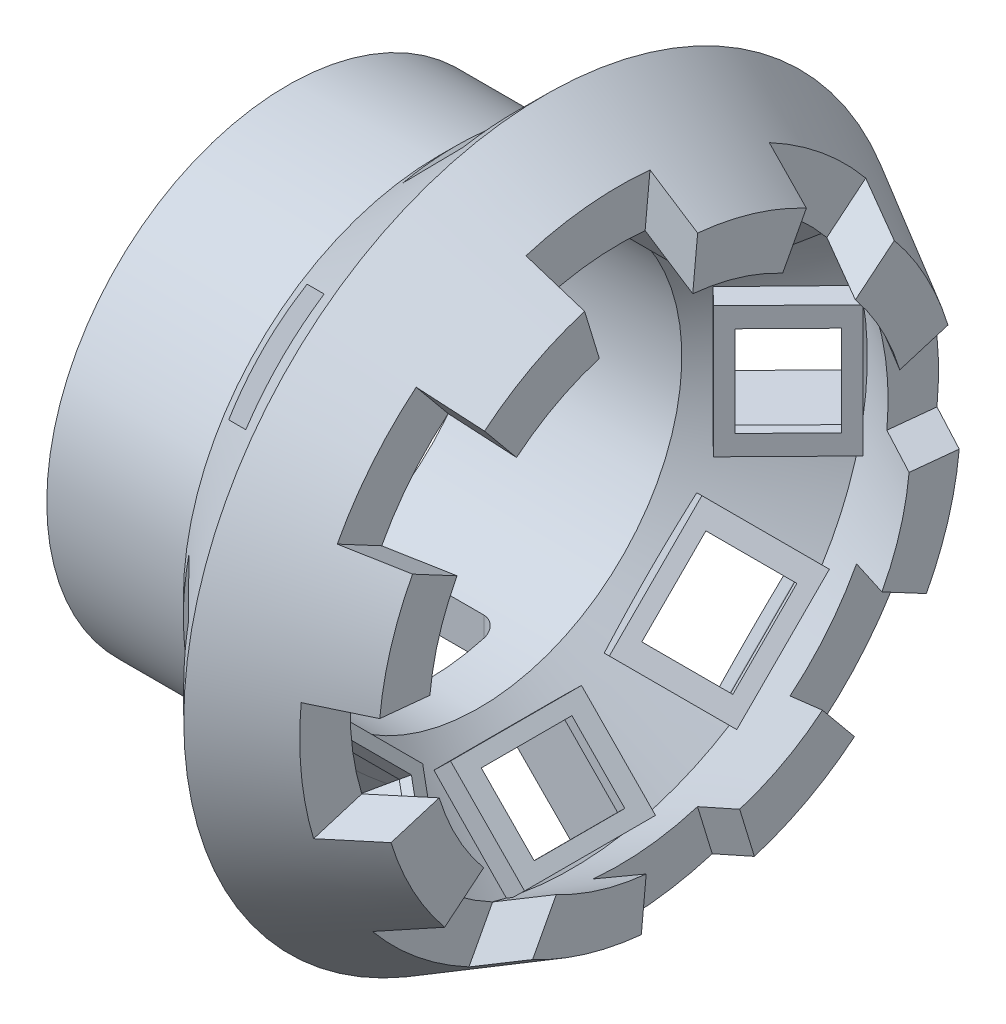
SolidWorks part; units mm, degrees
other "标注1"
sketch "草图8" plane through (-2.7147, -6.8585, 6.8585) normal (-0.2235, -0.0225, 0.9745) x (-0.1799, 0.9835, -0.0185)
ref_plane "前视基准面" through (0, 0, 0) normal (0, 0, 1) x (1, 0, 0)
ref_plane "上视基准面" through (0, 0, 0) normal (0, 1, 0) x (1, 0, 0)
ref_plane "右视基准面" through (0, 0, 0) normal (1, 0, 0) x (0, 0, -1)
sketch "草图1" plane through (0, 0, 0) normal (0, 0, 1) x (1, 0, 0)
  line L7 (8.0647, 7.1695) -> (11.04, 5.5)
  line L8 (11.04, 5.5) -> (11.04, 4.5)
  line L9 (11.04, 4.5) -> (8.6008, 5.8686)
  line L11 (7.54, 5.8) -> (7.54, 0) construction
  line L12 (0, 0) -> (8.3011, 0) construction
  line L13 (8.034, 5.3041) -> (7.54, 5.8) construction
  line L14 (6.755, 4.03) -> (8.6008, 5.8686)
  line L16 (11.04, 4.5) -> (11.04, -0.8919) construction
  line L17 (8.034, 5.3041) -> (11.109, 2.217) construction
  line L23 (5.955, 5.068) -> (8.0647, 7.1695)
  line L24 (6.0503, 4.03) -> (7.3502, 4.03) construction
  line L25 (5.955, 5.068) -> (5.955, 4.78)
  line L28 (6.0503, 4.03) -> (6.755, 4.03)
  line L31 (6.0503, 4.03) -> (2.955, 4.03)
  line L33 (5.955, 4.78) -> (2.955, 4.78)
  line L34 (2.955, 4.03) -> (2.955, 4.78)
  dimension "D1" = 4.5
  dimension "D2" = 3
  dimension "D3" = 0.8
  dimension "D4" = 4.03
  dimension "D5" = 0.8
  dimension "D6" = 0.7
  dimension "D7" = 5.8
  dimension "D8" = 1.3
  dimension "D9" = 1
  dimension "D10" = 3.5
  dimension "D13" = 0.75
revolve "旋转1" add sketch "草图1" angle 360 about L12
sketch "草图2" plane through (0, 0, 0) normal (0, 1, 0) x (1, 0, 0)
  line L1 (3.0145, -5.257) -> (4.0717, -5.257) construction
  line L8 (5.955, -5.068) -> (8.0647, -7.1695) construction
  line L9 (5.1803, -6.5082) -> (7.3988, -4.2897)
  line L10 (5.1803, -6.5082) -> (6.3824, -7.7103)
  line L11 (6.3824, -7.7103) -> (8.6009, -5.4918)
  line L12 (7.3988, -4.2897) -> (8.6009, -5.4918)
  line L13 (5.1803, -6.5082) -> (8.6009, -5.4918) construction
  line L14 (6.3824, -7.7103) -> (7.3988, -4.2897) construction
  line L15 (0, 0) -> (-4.3641, 0) construction
  line L16 (6.8906, -6) -> (5.7814, -7.1092) construction
  line L17 (5.955, -5.068) -> (8.0647, -7.1695) construction
  line L18 (5.955, -5.068) -> (8.0647, -7.1695) construction
  line L19 (5.955, -5.068) -> (8.0647, -7.1695) construction
  dimension "D1" = 45
  dimension "D2" = 1.7
  dimension "D3" = 6
extrude "切除-拉伸1" cut sketch "草图2" against normal mid plane 2.2
sketch "草图3" plane through (0, 0, 0) normal (0, 1, 0) x (1, 0, 0)
  line L0 (0, 0) -> (-2.7147, 0) construction
pattern_circular "阵列(圆周)1" count 8 over 360 about axis through (0, 0, 0) along (1, 0, 0) of "切除-拉伸1"
sketch "草图6" plane through (0, 0, 0) normal (0, 0, 1) x (1, 0, 0)
  line L0 (5.955, 5.068) -> (5.955, -5.068) construction
  line L1 (-2.939, 5.7136) -> (2.955, 5.7136)
  line L2 (-2.939, 5.7136) -> (-2.939, -5.5135)
  line L3 (-2.939, -5.5135) -> (2.955, -5.5135)
  line L4 (2.955, 5.7136) -> (2.955, -5.5135)
  line L5 (10.54, 7.4147) -> (14.0576, 7.4147)
  line L6 (10.54, 7.4147) -> (10.54, -7.7149)
  line L7 (10.54, -7.7149) -> (14.0576, -7.7149)
  line L8 (14.0576, 7.4147) -> (14.0576, -7.7149)
  line L9 (11.04, -5.5) -> (11.04, 5.5) construction
  dimension "D1" = 3
  dimension "D2" = 0.5
extrude "切除-拉伸2" cut sketch "草图6" against normal mid plane 20
ref_plane "基准面3" through (1.5037, -1.4741, 0) normal (-0.7141, 0.7001, 0) x (0, 0, 1)
sketch "草图7" plane through (1.5037, -1.4741, 0) normal (-0.7141, 0.7001, 0) x (0, 0, 1)
  line L10 (1.3, 10.1446) -> (-1.3, 10.1446)
  line L32 (-1.3, 10.1446) -> (-1.3, 8.0445)
  line L33 (-1.3, 8.0445) -> (1.3, 8.0445)
  line L34 (1.3, 8.0445) -> (1.3, 10.1446)
  line L35 (1.1, 9.9446) -> (-1.1, 9.9446)
  line L36 (-1.1, 9.9446) -> (-1.1, 8.2445)
  line L37 (-1.1, 8.2445) -> (1.1, 8.2445)
  line L38 (1.1, 8.2445) -> (1.1, 9.9446)
  dimension "D1" = 0.2
  dimension "D2" = 0.2
  dimension "D3" = 0.2
  dimension "D4" = 0.2
extrude "凸台-拉伸1" add sketch "草图7" along normal mid plane 0.6
sketch "草图11" plane through (1.7179, -1.6841, 0) normal (0.7141, -0.7001, 0) x (0, 0, -1)
  line L1 (-1.3, 10.1446) -> (1.3, 10.1446)
  line L2 (-1.3, 10.1446) -> (-1.3, 8.0445)
  line L3 (-1.3, 8.0445) -> (1.3, 8.0445)
  line L4 (1.3, 10.1446) -> (1.3, 8.0445)
  line L9 (-0.9, 9.8446) -> (0.9, 9.8446)
  line L10 (-0.9, 9.8446) -> (-0.9, 8.3445)
  line L11 (-0.9, 8.3445) -> (0.9, 8.3445)
  line L12 (0.9, 9.8446) -> (0.9, 8.3445)
  line L14 (-1.1, 9.9446) -> (1.1, 9.9446) construction
  line L15 (1.1, 8.2445) -> (-1.1, 8.2445) construction
  dimension "D1" = 0.4
  dimension "D2" = 0.4
  dimension "D3" = 0.1
  dimension "D4" = 0.1
extrude "凸台-拉伸2" add sketch "草图11" along normal blind 0.2
pattern_circular "阵列(圆周)2" count 8 over 360 about axis through (0, 0, 0) along (1, 0, 0) of "凸台-拉伸1", "凸台-拉伸2"
sketch "草图9" plane through (10.54, 0, 0) normal (1, 0, 0) x (0, 0, -1)
  line L2 (0, 0) -> (-2.1978, 7.2108)
  line L3 (0, 0) -> (0.729, 7.503)
  line L4 (0, 0) -> (3.5447, 6.6529)
  line L5 (0, 0) -> (5.8208, 4.7899)
  line L6 (0, 0) -> (7.2108, 2.1978)
  line L7 (0, 0) -> (7.503, -0.729)
  line L8 (0, 0) -> (6.6529, -3.5447)
  line L9 (0, 0) -> (4.7899, -5.8208)
  line L10 (0, 0) -> (2.1978, -7.2108)
  line L11 (0, 0) -> (-0.729, -7.503)
  line L12 (0, 0) -> (-3.5447, -6.6529)
  line L13 (0, 0) -> (-5.8208, -4.7899)
  line L14 (0, 0) -> (-7.2108, -2.1978)
  line L15 (0, 0) -> (-7.503, 0.729)
  line L16 (0, 0) -> (-6.6529, 3.5447)
  line L17 (0, 0) -> (-4.7899, 5.8208)
  arc A2 (-2.1978, 7.2108) -> (0.729, 7.503) centre (0, 0) cw
  arc A4 (3.5447, 6.6529) -> (5.8208, 4.7899) centre (0, 0) cw
  arc A5 (7.2108, 2.1978) -> (7.503, -0.729) centre (0, 0) cw
  arc A6 (6.6529, -3.5447) -> (4.7899, -5.8208) centre (0, 0) cw
  arc A7 (2.1978, -7.2108) -> (-0.729, -7.503) centre (0, 0) cw
  arc A8 (-3.5447, -6.6529) -> (-5.8208, -4.7899) centre (0, 0) cw
  arc A9 (-7.2108, -2.1978) -> (-7.503, 0.729) centre (0, 0) cw
  arc A10 (-6.6529, 3.5447) -> (-4.7899, 5.8208) centre (0, 0) cw
  point P21 (0, 0)
  circle M4 centre (0, 0) radius 5.7805
  circle M5 centre (0, 0) radius 4.7805
  dimension "D1" = 22.5
  dimension "D2" = 8
extrude "切除-拉伸3" cut sketch "草图9" against normal blind 1 contours L8 L9 M5 | L9 L8 M5 M4 | A6 L8 L9 M4 | A7 L10 L11 M4 | L11 L10 M5 M4 | L10 L11 M5 | A8 L12 L13 M4 | L13 L12 M5 M4 | L12 L13 M5 | A9 L14 L15 M4 | L15 L14 M5 M4 | L14 L15 M5 | A10 L16 L17 M4 | L17 L16 M5 M4 | L16 L17 M5 | L2 L3 M5 | L3 L2 M5 M4 | A2 L2 L3 M4 | A4 L4 L5 M4 | L5 L4 M5 M4 | L4 L5 M5 | A5 L6 L7 M4 | L7 L6 M5 M4 | L6 L7 M5
sketch "草图10" plane through (2.955, 0, 0) normal (-1, 0, 0) x (0, 0, 1)
  line L0 (0, 0) -> (0, -3.1283) construction
  line L1 (-1.4, -0.9467) -> (1.4, -0.9467)
  line L2 (-1.4, -0.9467) -> (-1.4, -5.3098)
  line L3 (-1.4, -5.3098) -> (1.4, -5.3098)
  line L4 (1.4, -0.9467) -> (1.4, -5.3098)
  line L5 (-1.4, -0.9467) -> (1.4, -5.3098) construction
  line L6 (-1.4, -5.3098) -> (1.4, -0.9467) construction
  point P0 (0, -3.1283)
  dimension "D1" = 2.8
extrude "切除-拉伸4" cut sketch "草图10" against normal offset from surface (2.8 mm away) 0.2 up to face at (5.955, 0, 4.78)
fillet "圆角1" radius 0.3 4 edges at (5.755, -4.1747, 1.4) (5.755, -4.1747, -1.4) (2.955, -4.1747, 1.4) (2.955, -4.1747, -1.4)
